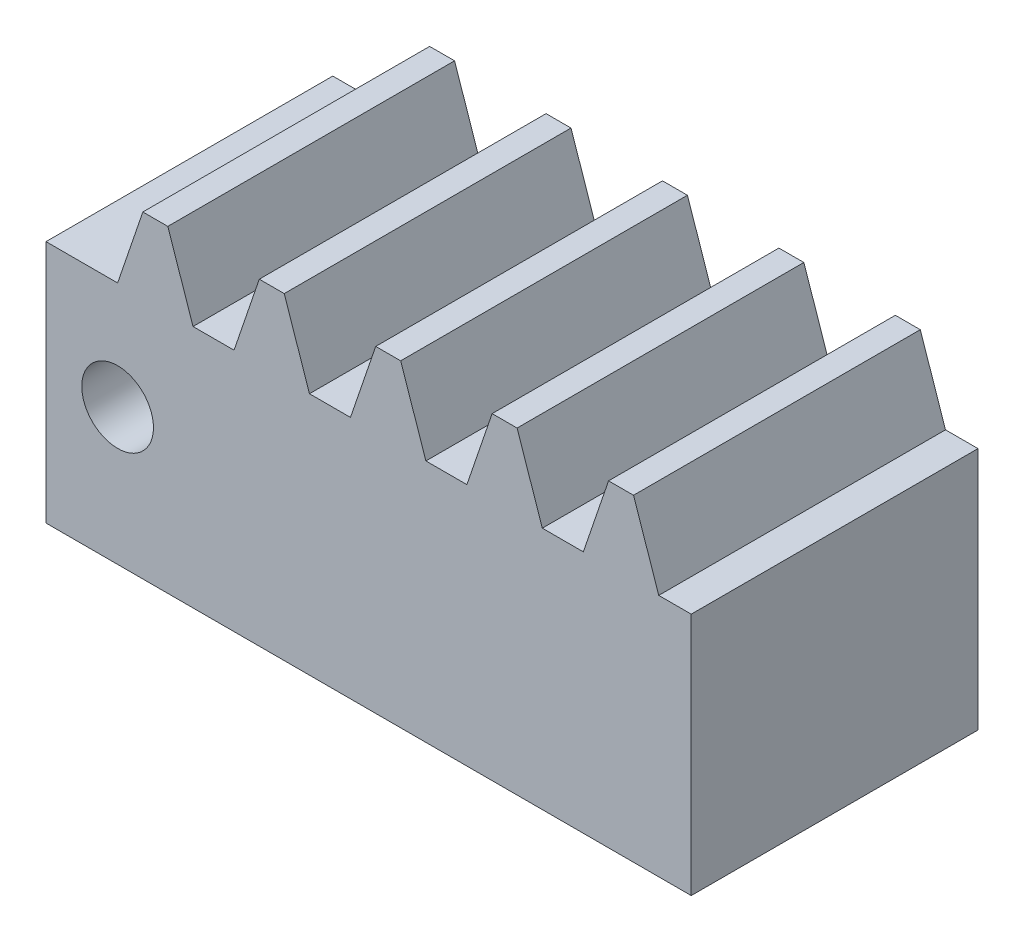
SolidWorks part; units mm, degrees
ref_plane "Front Plane" through (0, 0, 0) normal (0, 0, 1) x (1, 0, 0)
ref_plane "Top Plane" through (0, 0, 0) normal (0, 1, 0) x (1, 0, 0)
ref_plane "Right Plane" through (0, 0, 0) normal (1, 0, 0) x (0, 0, -1)
ref_plane "Plane4"
sketch "Sketch1" plane through (0, 0, 0) normal (0, 0, 1) x (1, 0, 0)
  line L0 (63.5, 21.59) -> (59.69, 21.59)
  line L1 (59.69, 21.59) -> (6.35, 21.59)
  line L2 (6.35, 21.59) -> (6.35, 0)
  line L3 (6.35, 0) -> (63.5, 0)
  line L4 (63.5, 0) -> (63.5, 21.59)
  line L5 (14.9286, 28.1544) -> (12.6934, 21.59)
  line L6 (12.6934, 21.59) -> (16.5034, 21.59)
  line L7 (16.5034, 21.59) -> (19.3736, 21.59)
  line L8 (19.3736, 21.59) -> (17.1384, 28.1544)
  line L9 (17.1384, 28.1544) -> (16.0335, 28.1544)
  line L10 (16.0335, 28.1544) -> (14.9286, 28.1544)
  line L11 (25.241, 28.1544) -> (23.0058, 21.59)
  line L12 (23.0058, 21.59) -> (29.686, 21.59)
  line L13 (29.686, 21.59) -> (27.4508, 28.1544)
  line L14 (27.4508, 28.1544) -> (26.3459, 28.1544)
  line L15 (26.3459, 28.1544) -> (25.241, 28.1544)
  line L16 (57.2831, 28.1544) -> (56.1782, 28.1544)
  line L17 (56.1782, 28.1544) -> (53.943, 21.59)
  line L18 (53.943, 21.59) -> (59.69, 21.59)
  line L19 (59.69, 21.59) -> (60.6232, 21.59)
  line L20 (60.6232, 21.59) -> (58.388, 28.1544)
  line L21 (58.388, 28.1544) -> (57.2831, 28.1544)
  line L22 (46.9707, 28.1544) -> (45.8658, 28.1544)
  line L23 (45.8658, 28.1544) -> (43.6306, 21.59)
  line L24 (43.6306, 21.59) -> (50.3108, 21.59)
  line L25 (50.3108, 21.59) -> (48.0756, 28.1544)
  line L26 (48.0756, 28.1544) -> (46.9707, 28.1544)
  line L27 (35.5534, 28.1544) -> (33.3182, 21.59)
  line L28 (33.3182, 21.59) -> (36.1867, 21.59)
  line L29 (36.1867, 21.59) -> (39.9967, 21.59)
  line L30 (39.9967, 21.59) -> (39.9984, 21.59)
  line L31 (39.9984, 21.59) -> (37.7632, 28.1544)
  line L32 (37.7632, 28.1544) -> (36.6583, 28.1544)
  line L33 (36.6583, 28.1544) -> (35.5534, 28.1544)
  circle A0 centre (12.6934, 12.0735) radius 3.175
extrude "Extrusion1" add sketch "Sketch1" along normal blind 25.4 contours L3 L4 L0 L1 L2 A0 | L9 L10 L5 L1 L8 | L14 L15 L11 L1 L13 | L20 L21 L16 L17 L1 L0 | L25 L26 L22 L23 L1 | L32 L33 L27 L1 L31
